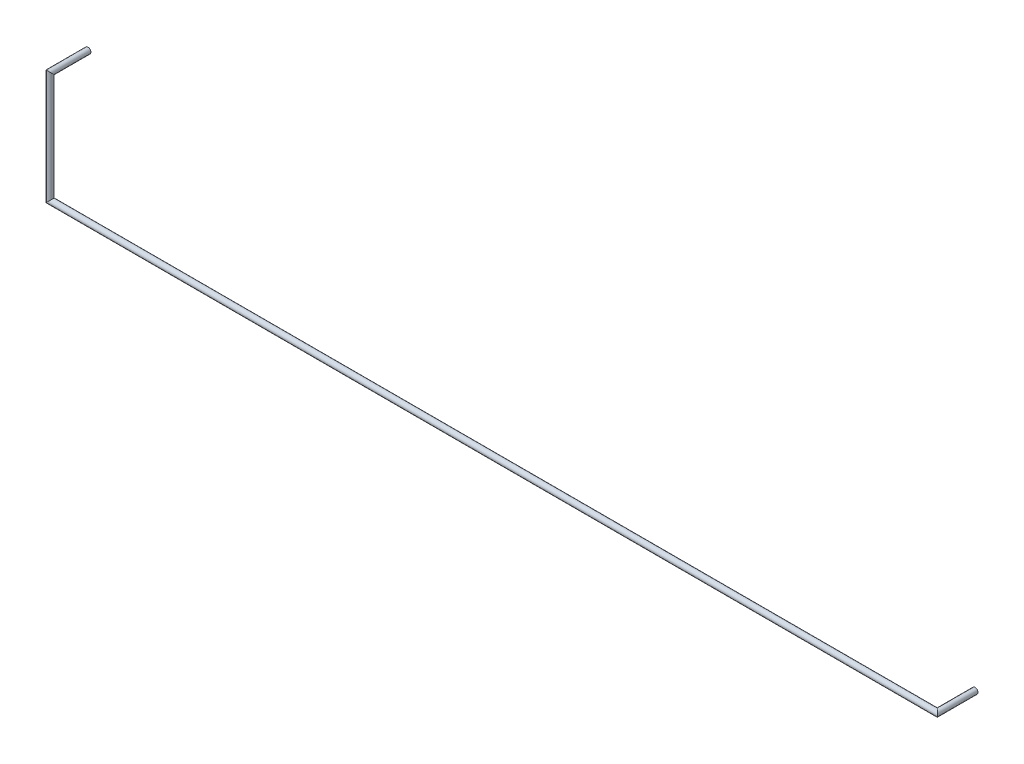
SolidWorks part; units mm, degrees
ref_plane "Front Plane" through (0, 0, 0) normal (0, 0, 1) x (1, 0, 0)
ref_plane "Top Plane" through (0, 0, 0) normal (0, 1, 0) x (1, 0, 0)
ref_plane "Right Plane" through (0, 0, 0) normal (1, 0, 0) x (0, 0, -1)
sketch3d "3DSketch3"
  line L0 (0, 0, 0) -> (0, 0, 2.6)
  line L1 (0, 0, 2.6) -> (0, -7.62, 2.6)
  line L2 (0, -7.62, 2.6) -> (60.96, -7.62, 2.6)
  line L3 (60.96, -7.62, 2.6) -> (60.96, -7.62, 0)
  point P6 (0, -7.0598, 2.6)
  dimension "D2" = 2.6
  dimension "D1" = 2.6
  dimension "D4" = 60.96
  dimension "D3" = 7.62
sweep "Sweep1" add path "3DSketch3" circular profile diameter 0.4 parameters "D3"=0.4
equation "\"D2@3DSketch3\"=\"D1@3DSketch3\""
equation "\"D4@3DSketch3\"=2.54*24"
